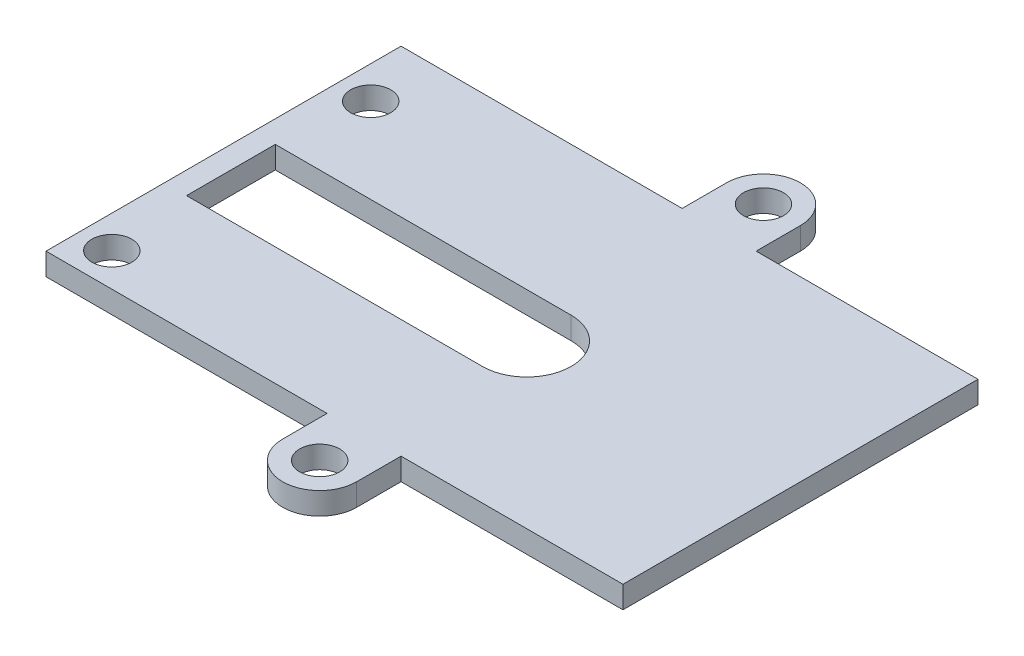
SolidWorks part; units mm, degrees
ref_plane "Front Plane" through (0, 0, 0) normal (0, 0, 1) x (1, 0, 0)
ref_plane "Top Plane" through (0, 0, 0) normal (0, 1, 0) x (1, 0, 0)
ref_plane "Right Plane" through (0, 0, 0) normal (1, 0, 0) x (0, 0, -1)
sketch "Sketch1" plane through (0, 0, 0) normal (0, 1, 0) x (1, 0, 0)
  line L0 (0, 0) -> (0, 29.672) construction
  line L1 (-17.5, 12) -> (17.5, 12)
  line L2 (-17.5, 12) -> (-17.5, -12)
  line L3 (-17.5, -12) -> (17.5, -12)
  line L4 (17.5, 12) -> (17.5, -12)
  line L5 (-17.5, 12) -> (17.5, -12) construction
  line L6 (-17.5, -12) -> (17.5, 12) construction
  line L7 (0, 0) -> (23.9228, 0) construction
  line L8 (-2.5, 15) -> (-2.5, 12)
  line L9 (2.5, 15) -> (2.5, 12)
  line L10 (2.5, -15) -> (2.5, -12)
  line L11 (-2.5, -15) -> (-2.5, -12)
  line L12 (12.5, 23.3064) -> (12.5, -18.3833) construction
  line L13 (-19.3, 26.6031) -> (-19.3, -22.3482) construction
  line L14 (0, 0) -> (-41.9615, 0) construction
  line L15 (-17.5, 12) -> (-21.5, 12)
  line L16 (-21.5, 12) -> (-21.5, -12)
  line L17 (-21.5, -12) -> (-17.5, -12)
  line L18 (-41.9615, -1) -> (23.9228, -1) construction
  circle A0 centre (0, 15) radius 1.35
  circle A1 centre (0, 15) radius 2.5
  circle A2 centre (0, -15) radius 1.35
  circle A3 centre (0, -15) radius 2.5
  circle A7 centre (0, -1) radius 3
  circle A8 centre (-19.3, 7.75) radius 1.35
  circle A9 centre (-19.3, -9.75) radius 1.35
  point P0 (0, 0)
  dimension "D3" = 2.7
  dimension "D4" = 3
  dimension "D5" = 5
  dimension "D7" = 1
  dimension "D10" = 6
  dimension "D11" = 2.7
  dimension "D12" = 8.75
  dimension "D1" = 24
  dimension "D2" = 35
  dimension "D6" = 5
  dimension "D8" = 31.8
  dimension "D9" = 4
extrude "Boss-Extrude1" add sketch "Sketch1" along normal blind 1.5 contours L4 L1 L2 L3 A7 | L11 A3 L10 L3 | A3 A2 | A1 L8 L1 L9 | A1 A0 | L16 L17 L2 L15 A8 A9
sketch "Sketch2" plane through (0, 1.5, 0) normal (0, 1, 0) x (1, 0, 0)
  line L0 (0, 2) -> (-20, 2)
  line L1 (-20, 2) -> (-20, -4)
  line L2 (-20, -4) -> (0, -4)
  circle A0 centre (0, -1) radius 3 construction
  arc A1 (0, 2) -> (0, -4) centre (0, -1) cw
  dimension "D1" = 20
extrude "Cut-Extrude1" cut sketch "Sketch2" against normal blind 10
